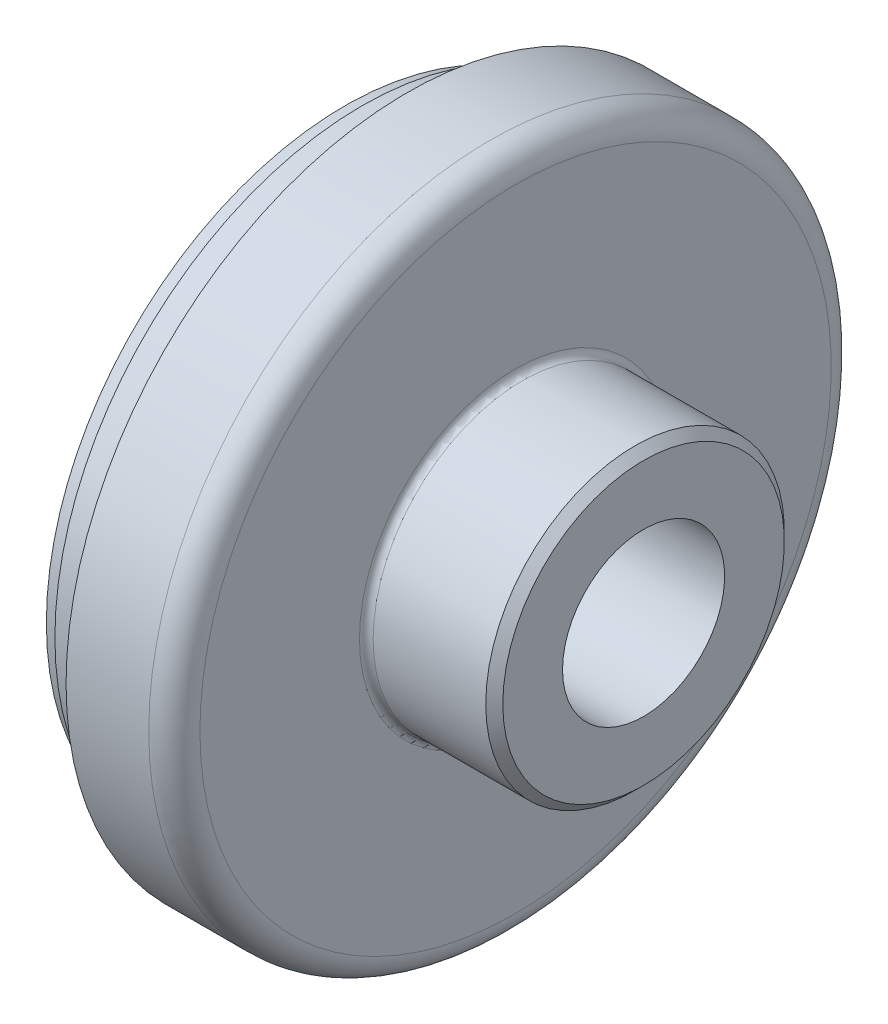
SolidWorks part; units mm, degrees
ref_plane "Front" through (0, 0, 0) normal (0, 0, 1) x (1, 0, 0)
ref_plane "Top" through (0, 0, 0) normal (0, 1, 0) x (1, 0, 0)
ref_plane "Right" through (0, 0, 0) normal (1, 0, 0) x (0, 0, -1)
sketch "Sketch1" plane through (0, 0, 0) normal (0, 0, 1) x (1, 0, 0)
  line L0 (-31.2769, 0) -> (34.1365, 0) construction
  line L1 (0, 9.5) -> (35, 9.5)
  line L2 (35, 9.5) -> (35, 16.5)
  line L3 (35, 16.5) -> (34, 17.5)
  line L5 (34, 17.5) -> (20.8, 17.5)
  line L6 (20, 18.3) -> (20, 37)
  line L7 (17, 40) -> (7.3094, 40)
  line L8 (7.3094, 40) -> (5, 36)
  line L9 (5, 36) -> (2, 36)
  line L10 (2, 36) -> (2, 35)
  line L11 (2, 35) -> (0, 35)
  line L12 (0, 35) -> (0, 9.5)
  arc A0 (20, 37) -> (17, 40) centre (17, 37) ccw
  arc A1 (20.8, 17.5) -> (20, 18.3) centre (20.8, 18.3) cw
  dimension "D14" = 3
  dimension "D15" = 0.8
  dimension "D2" = 35
  dimension "D3" = 19
  dimension "D4" = 2
  dimension "D5" = 3
  dimension "D6" = 30
  dimension "D7" = 70
  dimension "D8" = 20
  dimension "D9" = 35
  dimension "D10" = 80
  dimension "D11" = 72
  dimension "D12" = 45
  dimension "D13" = 1
revolve "Base-Revolve" add sketch "Sketch1" angle 360 about L0
cosmetic thread "Cosmetic Thread5" parameters "D1"=15, "D2"=20.995
